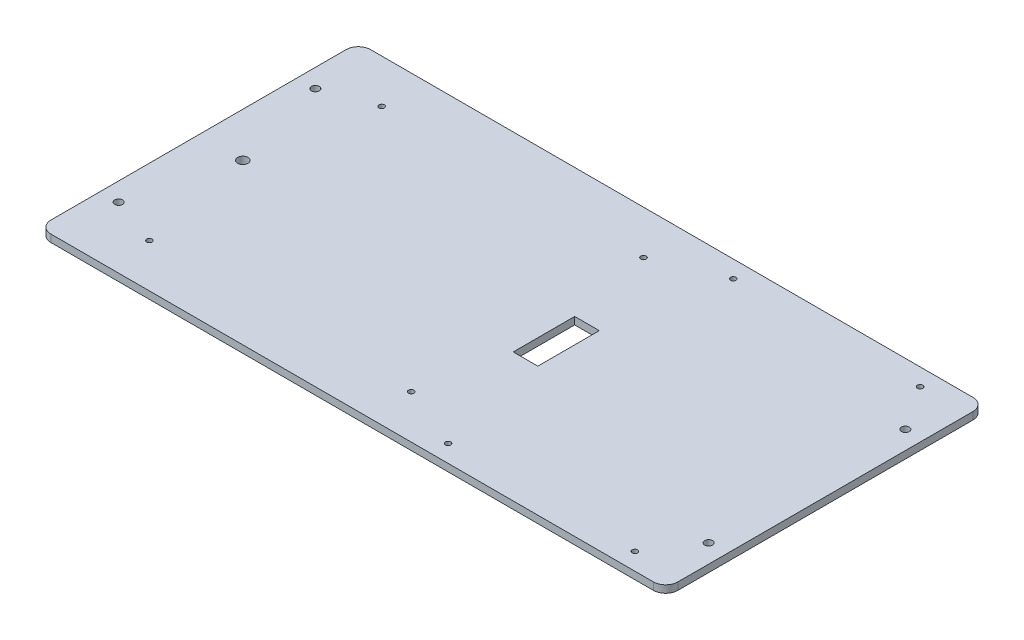
SolidWorks part; units mm, degrees
material "Acrylic (Medium-high impact)"
ref_plane "Front Plane" through (0, 0, 0) normal (0, 0, 1) x (1, 0, 0)
ref_plane "Top Plane" through (0, 0, 0) normal (0, 1, 0) x (1, 0, 0)
ref_plane "Right Plane" through (0, 0, 0) normal (1, 0, 0) x (0, 0, -1)
sketch "Sketch1" plane through (0, 0, 0) normal (0, 1, 0) x (1, 0, 0)
  line L0 (127.5, 0) -> (-127.5, 0) construction
  line L1 (-127.5, -65) -> (127.5, -65)
  line L2 (-127.5, -65) -> (-127.5, 65)
  line L3 (-127.5, 65) -> (127.5, 65)
  line L4 (127.5, -65) -> (127.5, 65)
  line L5 (-127.5, -65) -> (127.5, 65) construction
  line L6 (-127.5, 65) -> (127.5, -65) construction
  line L7 (0, -65) -> (0, 65) construction
  line L8 (70, -60) -> (70, 60) construction
  line L9 (13, -12.5) -> (23, -12.5)
  line L10 (13, -12.5) -> (13, 12.5)
  line L11 (13, 12.5) -> (23, 12.5)
  line L12 (23, -12.5) -> (23, 12.5)
  line L13 (13, -12.5) -> (23, 12.5) construction
  line L14 (13, 12.5) -> (23, -12.5) construction
  line L15 (30, -60) -> (110, -60) construction
  line L16 (30, -60) -> (30, 60) construction
  line L17 (30, 60) -> (110, 60) construction
  line L18 (110, -60) -> (110, 60) construction
  line L20 (-94, -29) -> (0, -29) construction
  line L21 (-94, -29) -> (-94, 29) construction
  line L22 (-94, 29) -> (0, 29) construction
  line L23 (0, -29) -> (0, 29) construction
  line L24 (-94, -29) -> (0, 29) construction
  line L25 (-94, 29) -> (0, -29) construction
  line L26 (-100.25, -47.25) -> (6.25, -47.25) construction
  line L27 (-100.25, -47.25) -> (-100.25, 47.25) construction
  line L28 (-100.25, 47.25) -> (6.25, 47.25) construction
  line L29 (6.25, -47.25) -> (6.25, 47.25) construction
  line L30 (-100.25, -47.25) -> (6.25, 47.25) construction
  line L31 (-100.25, 47.25) -> (6.25, -47.25) construction
  circle A0 centre (120, -40) radius 1.6
  circle A1 centre (-120, -40) radius 1.6
  circle A2 centre (120, 40) radius 1.6
  circle A3 centre (-120, 40) radius 1.6
  circle A4 centre (-94, 29) radius 1.1 construction
  circle A7 centre (-94, -29) radius 1.1 construction
  circle A9 centre (30, 38) radius 1.1 construction
  circle A10 centre (86, 38) radius 1.1 construction
  circle A11 centre (86, -38) radius 1.1 construction
  circle A12 centre (30, -38) radius 1.1 construction
  circle A13 centre (0, 29) radius 1.1 construction
  circle A14 centre (0, -29) radius 1.1 construction
  circle A15 centre (32, -58) radius 1.1
  circle A16 centre (108, -58) radius 1.1
  circle A17 centre (108, 58) radius 1.1
  circle A18 centre (32, 58) radius 1.1
  circle A19 centre (-100.25, 47.25) radius 1.1
  circle A20 centre (6.25, 47.25) radius 1.1
  circle A21 centre (-100.25, -47.25) radius 1.1
  circle A22 centre (6.25, -47.25) radius 1.1
  circle A23 centre (108.5, 0) radius 2.1 construction
  circle A24 centre (-109.5, 0) radius 2.1
  point P0 (0, 0)
  point P30 (18, 0)
  point P51 (-47, 0)
  point P59 (-47, 0)
  dimension "D3" = 3.2
  dimension "D6" = 2.2
  dimension "D9" = 2.2
  dimension "D11" = 2.2
  dimension "D12" = 2.2
  dimension "D8" = 18
  dimension "D23" = 2.2
  dimension "D28" = 2.2
  dimension "D29" = 4.2
  dimension "D31" = 4.2
  dimension "D1" = 130
  dimension "D2" = 255
  dimension "D4" = 7.5
  dimension "D5" = 40
  dimension "D7" = 29
  dimension "D10" = 0
  dimension "D13" = 56
  dimension "D14" = 30
  dimension "D15" = 38
  dimension "D16" = 10
  dimension "D17" = 25
  dimension "D18" = 94
  dimension "D19" = 29
  dimension "D20" = 120
  dimension "D21" = 80
  dimension "D22" = 30
  dimension "D24" = 2
  dimension "D25" = 2
  dimension "D26" = 106.5
  dimension "D27" = 94.5
  dimension "D30" = 19
  dimension "D32" = 18
extrude "Boss-Extrude1" add sketch "Sketch1" along normal blind 3
fillet "Fillet1" radius 5 4 edges at (-127.5, 1.5, -65) (127.5, 1.5, -65) (127.5, 1.5, 65) (-127.5, 1.5, 65)
